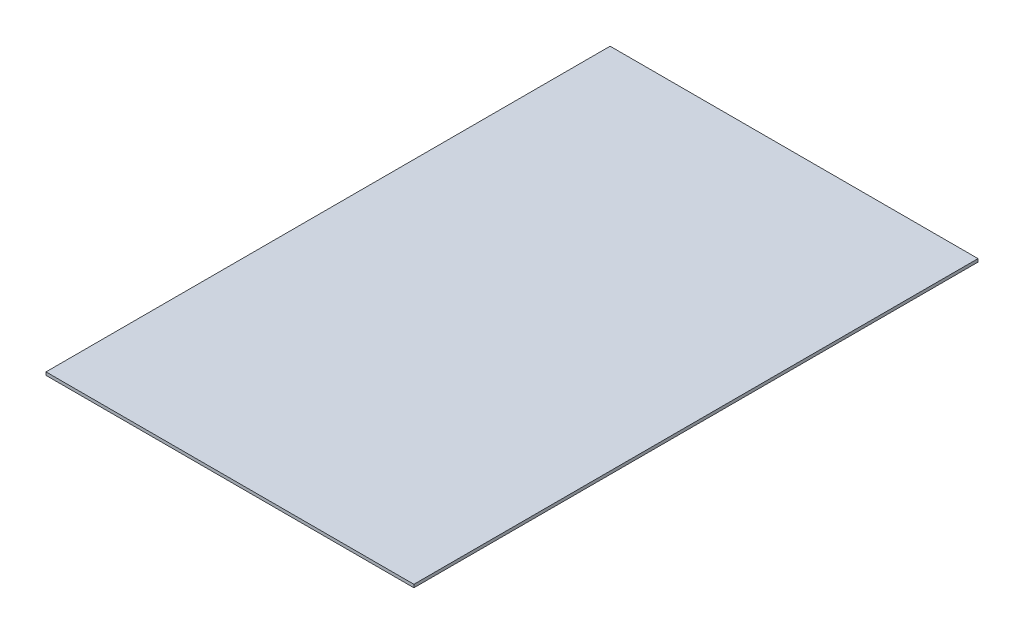
SolidWorks part; units mm, degrees
ref_plane "Front Plane" through (0, 0, 0) normal (0, 0, 1) x (1, 0, 0)
ref_plane "Top Plane" through (0, 0, 0) normal (0, 1, 0) x (1, 0, 0)
ref_plane "Right Plane" through (0, 0, 0) normal (1, 0, 0) x (0, 0, -1)
sketch "Sketch1" plane through (0, 0, 0) normal (0, 1, 0) x (1, 0, 0)
  line L1 (0, 0) -> (600, 0)
  line L2 (0, 0) -> (0, 920)
  line L3 (0, 920) -> (600, 920)
  line L4 (600, 0) -> (600, 920)
  dimension "D1" = 600
  dimension "D2" = 920
extrude "Boss-Extrude1" add sketch "Sketch1" along normal blind 5
